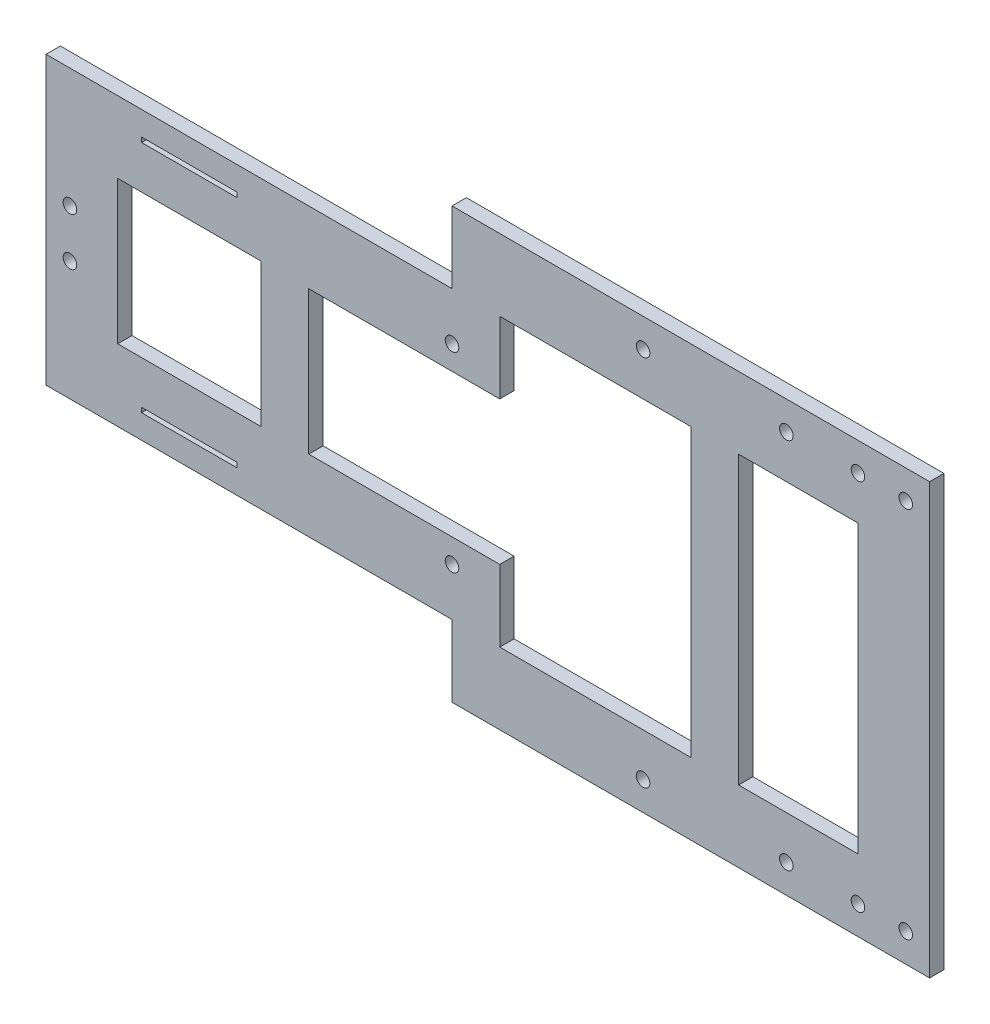
SolidWorks part; units mm, degrees
ref_plane "Front Plane" through (0, 0, 0) normal (0, 0, 1) x (1, 0, 0)
ref_plane "Top Plane" through (0, 0, 0) normal (0, 1, 0) x (1, 0, 0)
ref_plane "Right Plane" through (0, 0, 0) normal (1, 0, 0) x (0, 0, -1)
sketch "Sketch1" plane through (0, 0, 0) normal (0, 0, 1) x (1, 0, 0)
  line L0 (91.2766, 0) -> (-138.1947, 0) construction
  line L1 (0, 60.9532) -> (0, -61.5105) construction
  line L2 (-55, 45) -> (45, 45)
  line L3 (-140, 30) -> (-140, -30)
  line L4 (-55, -45) -> (45, -45)
  line L5 (45, 45) -> (45, -45)
  line L6 (-140, 30) -> (-55, 30)
  line L7 (-55, 30) -> (-55, 45)
  line L8 (-140, -30) -> (-55, -30)
  line L9 (-55, -30) -> (-55, -45)
  line L16 (-15, 30) -> (-45, 30)
  line L17 (-45, 30) -> (-45, 15)
  line L23 (30.0001, 30) -> (30.0001, -30)
  line L28 (-125, 15) -> (-125, -15)
  line L29 (-45, 15) -> (-85, 15)
  line L32 (-45, -15) -> (-85, -15)
  line L33 (-45, -15) -> (-45, -30)
  line L34 (-100, -25) -> (-100, -24)
  line L35 (-120, 25) -> (-100, 25)
  line L36 (-120, 25) -> (-120, 24)
  line L37 (-120, 24) -> (-100, 24)
  line L38 (-100, 25) -> (-100, 24)
  line L39 (-120, -24) -> (-100, -24)
  line L40 (-120, -25) -> (-120, -24)
  line L41 (-120, -25) -> (-100, -25)
  line L42 (-95, 15) -> (-95, -15)
  line L43 (-85, 15) -> (-85, -15)
  line L44 (-95, 15) -> (-125, 15)
  line L45 (-95, -15) -> (-125, -15)
  line L46 (-15, 30) -> (-5, 30)
  line L47 (-5, 30) -> (-5, -30)
  line L49 (-45, -30) -> (-5, -30)
  line L50 (5, 30) -> (5, -30)
  line L51 (5, 30) -> (30.0001, 30)
  line L52 (5, -30) -> (30.0001, -30)
  circle A1 centre (15, 39) radius 1.42
  circle A2 centre (-15, 39) radius 1.42
  circle A3 centre (-15, -39) radius 1.42
  circle A4 centre (15, -39) radius 1.42
  circle A6 centre (30.0001, 39.0563) radius 1.42
  circle A7 centre (40, 39.0133) radius 1.42
  circle A8 centre (-55, 20) radius 1.42
  circle A9 centre (-55, -20) radius 1.42
  circle A10 centre (40, -39.0133) radius 1.42
  circle A11 centre (30.0001, -39.0563) radius 1.42
  circle A12 centre (-135, 5) radius 1.42
  circle A13 centre (-135, -5) radius 1.42
  point P21 (-55, 37.5)
  point P31 (-55, -37.5)
  point P44 (-63, 0)
  point P45 (-93, 0)
  point P50 (-15, 0)
  point P51 (-45, 0)
  point P61 (22.5, -30)
  point P62 (30.0001, 0)
  point P64 (-125, 0)
  dimension "D5" = 15
  dimension "D7" = 10
  dimension "D14" = 80
  dimension "D1" = 45
  dimension "D2" = 45
  dimension "D3" = 45
  dimension "D4" = 140
  dimension "D6" = 6
  dimension "D8" = 55
  dimension "D9" = 20
  dimension "D10" = 5
  dimension "D11" = 5
  dimension "D12" = 5
  dimension "D13" = 30
  dimension "D15" = 15
  dimension "D16" = 1
  dimension "D17" = 10
  dimension "D18" = 25
  dimension "D19" = 30
  dimension "D20" = 20
  dimension "D21" = 20
  dimension "D22" = 30
  dimension "D23" = 10
  dimension "D24" = 5
extrude "Boss-Extrude1" add sketch "Sketch1" along normal blind 3
